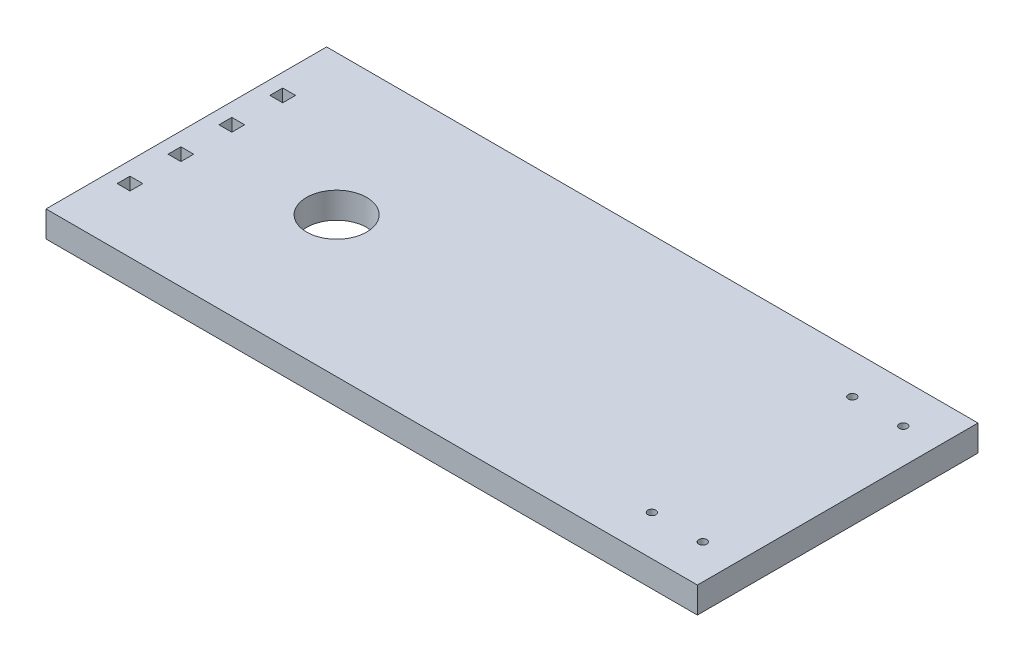
SolidWorks part; units mm, degrees
ref_plane "Front Plane" through (0, 0, 0) normal (0, 0, 1) x (1, 0, 0)
ref_plane "Top Plane" through (0, 0, 0) normal (0, 1, 0) x (1, 0, 0)
ref_plane "Right Plane" through (0, 0, 0) normal (1, 0, 0) x (0, 0, -1)
sketch "Sketch1" plane through (0, 0, 0) normal (0, 1, 0) x (1, 0, 0)
  line L1 (-16.25, -7) -> (16.25, -7)
  line L2 (-16.25, -7) -> (-16.25, 7)
  line L3 (-16.25, 7) -> (16.25, 7)
  line L4 (16.25, -7) -> (16.25, 7)
  line L5 (-16.25, -7) -> (16.25, 7) construction
  line L6 (-16.25, 7) -> (16.25, -7) construction
  point P0 (0, 0)
  dimension "D1" = 14
  dimension "D2" = 32.5
extrude "Boss-Extrude1" add sketch "Sketch1" along normal blind 1.3
sketch "Sketch2" plane through (0, 1.3, 0) normal (0, 1, 0) x (1, 0, 0)
  line L0 (16.25, 0) -> (-16.25, 0) construction
  line L1 (16.25, -7) -> (16.25, 7) construction
  line L2 (-16.25, 7) -> (-16.25, -7) construction
  line L3 (14.52, -5) -> (11.98, -5) construction
  line L4 (13.25, -5) -> (13.25, 0) construction
  line L5 (-15.25, 7) -> (-15.25, -7) construction
  line L6 (16.25, 7) -> (-16.25, 7) construction
  line L7 (-16.25, -7) -> (16.25, -7) construction
  line L9 (-15.57, 4.13) -> (-14.93, 4.13)
  line L10 (-15.57, 4.13) -> (-15.57, 3.49)
  line L11 (-15.57, 3.49) -> (-14.93, 3.49)
  line L12 (-14.93, 4.13) -> (-14.93, 3.49)
  line L13 (-15.57, 4.13) -> (-14.93, 3.49) construction
  line L14 (-15.57, 3.49) -> (-14.93, 4.13) construction
  line L15 (-15.57, 1.59) -> (-14.93, 1.59)
  line L16 (-15.57, 1.59) -> (-15.57, 0.95)
  line L17 (-15.57, 0.95) -> (-14.93, 0.95)
  line L18 (-14.93, 1.59) -> (-14.93, 0.95)
  line L19 (-15.57, 1.59) -> (-14.93, 0.95) construction
  line L20 (-15.57, 0.95) -> (-14.93, 1.59) construction
  line L21 (-15.57, -0.95) -> (-14.93, -0.95)
  line L22 (-15.57, -0.95) -> (-15.57, -1.59)
  line L23 (-15.57, -1.59) -> (-14.93, -1.59)
  line L24 (-14.93, -0.95) -> (-14.93, -1.59)
  line L25 (-15.57, -0.95) -> (-14.93, -1.59) construction
  line L26 (-15.57, -1.59) -> (-14.93, -0.95) construction
  line L27 (-15.57, -3.49) -> (-14.93, -3.49)
  line L28 (-15.57, -3.49) -> (-15.57, -4.13)
  line L29 (-15.57, -4.13) -> (-14.93, -4.13)
  line L30 (-14.93, -3.49) -> (-14.93, -4.13)
  line L31 (-15.57, -3.49) -> (-14.93, -4.13) construction
  line L32 (-15.57, -4.13) -> (-14.93, -3.49) construction
  circle A0 centre (14.52, -5) radius 0.2
  circle A1 centre (11.98, -5) radius 0.2
  circle A2 centre (11.98, 5) radius 0.2
  circle A3 centre (14.52, 5) radius 0.2
  point P22 (-15.25, 3.81)
  point P27 (-15.25, 1.27)
  point P32 (-15.25, -1.27)
  point P37 (-15.25, -3.81)
  dimension "D1" = 2.54
  dimension "D2" = 0.4
  dimension "D3" = 5
  dimension "D4" = 3
  dimension "D5" = 1
  dimension "D6" = 2.54
  dimension "D7" = 2.54
  dimension "D8" = 2.54
  dimension "D9" = 0.64
  dimension "D10" = 0.64
  dimension "D11" = 1.27
extrude "Cut-Extrude1" cut sketch "Sketch2" against normal through all
sketch "Sketch3" plane through (0, 1.3, 0) normal (0, 1, 0) x (1, 0, 0)
  line L0 (16.25, 0) -> (-16.25, 0) construction
  line L1 (16.25, -7) -> (16.25, 7) construction
  line L2 (-16.25, 7) -> (-16.25, -7) construction
  circle A0 centre (-8.75, 0) radius 1.5
  point P8 (-10.25, 0)
  dimension "D1" = 3
  dimension "D2" = 6
extrude "Cut-Extrude2" cut sketch "Sketch3" against normal blind 10
